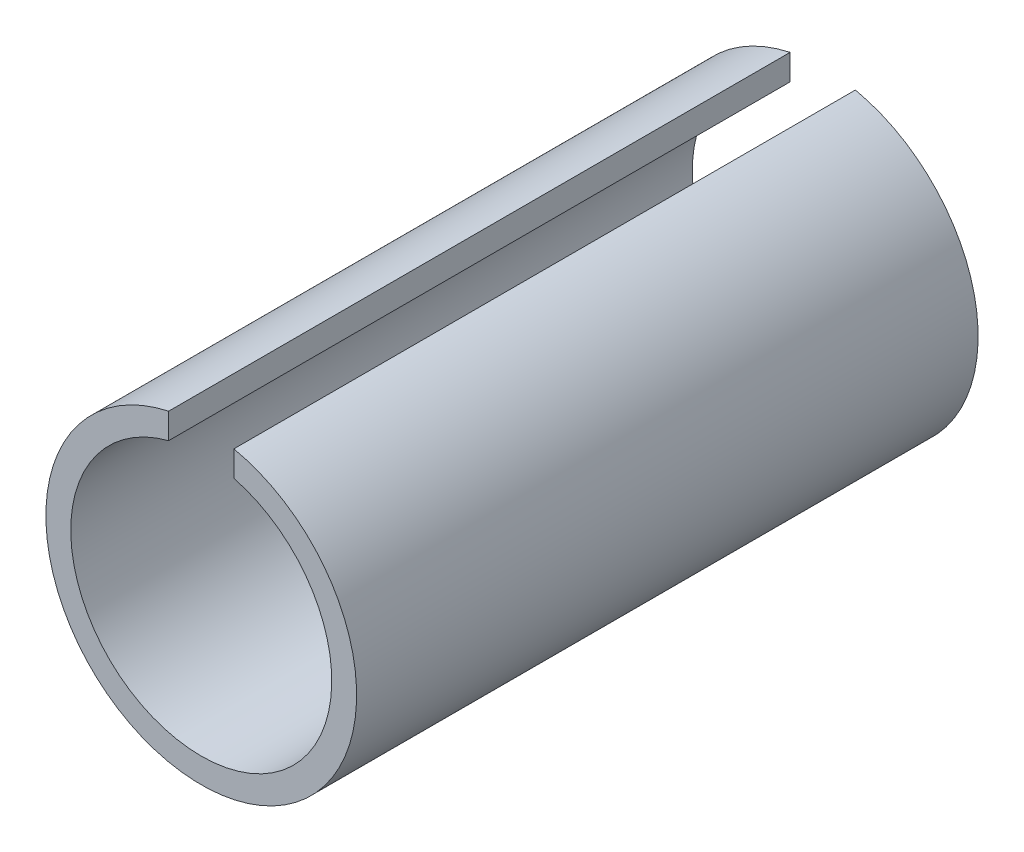
SolidWorks part; units mm, degrees
material "6061-T6 (SS)"
ref_plane "Front Plane" through (0, 0, 0) normal (0, 0, 1) x (1, 0, 0)
ref_plane "Top Plane" through (0, 0, 0) normal (0, 1, 0) x (1, 0, 0)
ref_plane "Right Plane" through (0, 0, 0) normal (1, 0, 0) x (0, 0, -1)
sketch "Sketch1" plane through (0, 0, 0) normal (0, 0, 1) x (1, 0, 0)
  line L0 (-1, 3.873) -> (0, 0) construction
  line L1 (0, 0) -> (1, 3.873) construction
  line L2 (-1, 3.873) -> (-1, 4.6563)
  line L4 (1, 3.873) -> (1, 4.6563)
  arc A0 (-1, 4.6563) -> (1, 4.6563) centre (0, 0) ccw
  arc A1 (-1, 3.873) -> (1, 3.873) centre (0, 0) ccw
  point P1 (0, 0)
  dimension "D1" = 9.525
  dimension "D2" = 8
  dimension "D3" = 2
extrude "Boss-Extrude1" add sketch "Sketch1" along normal blind 19.05
